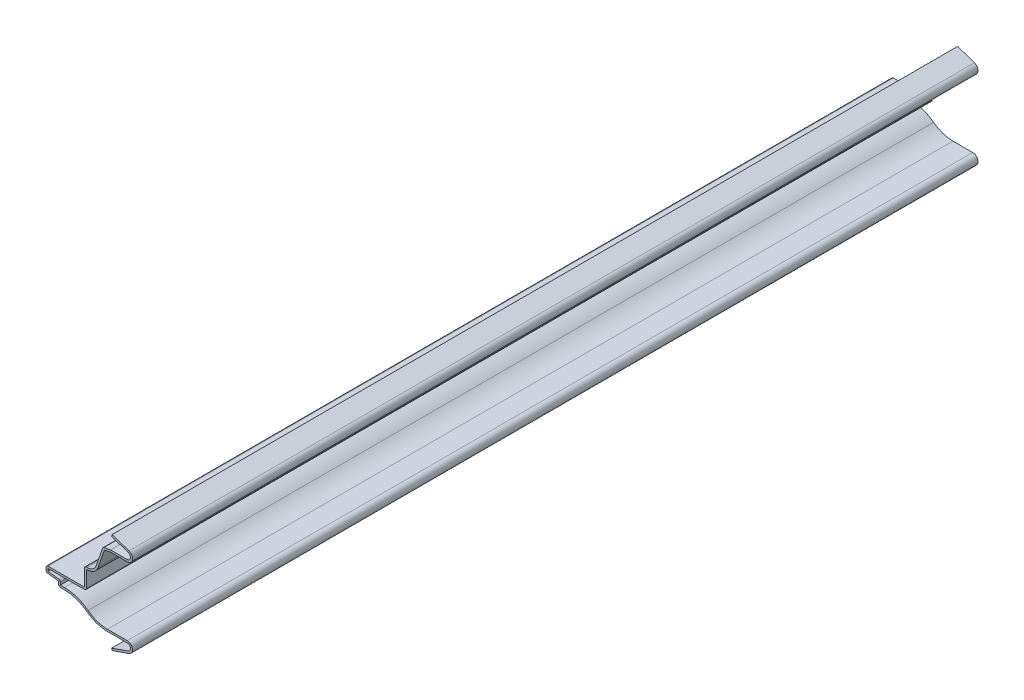
SolidWorks part; units mm, degrees
ref_plane "Front Plane" through (0, 0, 0) normal (0, 0, 1) x (1, 0, 0)
ref_plane "Top Plane" through (0, 0, 0) normal (0, 1, 0) x (1, 0, 0)
ref_plane "Right Plane" through (0, 0, 0) normal (1, 0, 0) x (0, 0, -1)
sketch "Sketch1" plane through (0, 0, 0) normal (0, 0, 1) x (1, 0, 0)
  line L0 (0, 0) -> (0, 50.0063) construction
  line L1 (9.7813, 50.0062) -> (1.1588, 47.0104)
  line L2 (1.7249, 43.6562) -> (10.3187, 43.6562)
  line L3 (10.3187, 43.6562) -> (14.2735, 42.8625)
  line L4 (14.2735, 42.8625) -> (17.7123, 32.9651)
  line L5 (23.7985, 29.7656) -> (23.7985, 20.2406)
  line L6 (23.7985, 20.2406) -> (43.6562, 20.2406)
  line L7 (43.6562, 20.2406) -> (43.6562, 17.0656)
  line L8 (43.6562, 17.0656) -> (37.3062, 16.2719)
  line L9 (37.3062, 16.2719) -> (37.3062, 13.8906)
  line L10 (11.9062, 6.35) -> (10.3187, 6.35)
  line L11 (1.1588, 2.9958) -> (9.7813, 0)
  line L12 (0, 0) -> (9.7813, 0) construction
  line L13 (0, 50.0063) -> (9.7813, 50.0062) construction
  line L14 (0, 25.0031) -> (23.7985, 25.0031) construction
  line L15 (37.3062, 13.8906) -> (34.1312, 13.8906)
  line L16 (10.3187, 6.35) -> (1.7249, 6.35)
  line L17 (23.7985, 29.7656) -> (22.211, 29.7656)
  arc A0 (1.1588, 47.0104) -> (1.7249, 43.6562) centre (1.7249, 45.3811) ccw
  arc A1 (22.211, 29.7656) -> (17.7123, 32.9651) centre (22.211, 34.5281) cw
  arc A2 (34.1312, 13.8906) -> (22.5389, 9.9575) centre (34.1312, -5.1594) ccw
  arc A3 (22.5389, 9.9575) -> (11.9062, 6.35) centre (11.9062, 23.8229) cw
  arc A4 (1.7249, 6.35) -> (1.1588, 2.9958) centre (1.7249, 4.6251) ccw
  arc A5 (1.5293, 7.359) -> (0.787, 2.0497) centre (1.7249, 4.6251) ccw construction
  arc A6 (1.7249, 7.366) -> (0.8253, 2.0361) centre (1.7249, 4.6251) ccw construction
  point P24 (0, 0)
  point P25 (1.3652, 5.6507)
  point P27 (10.3187, 0)
  dimension "D5" = 6.35
  dimension "D6" = 10.3187
  dimension "D14" = 19.05
  dimension "D16" = 4.7625
  dimension "D1" = 37.3062
  dimension "D2" = 0.7937
  dimension "D3" = 9.1281
  dimension "D7" = 9.525
  dimension "D8" = 13.8906
  dimension "D9" = 9.525
  dimension "D10" = 3.175
  dimension "D11" = 0.7937
  dimension "D12" = 3.175
  dimension "D13" = 7.5406
  dimension "D15" = 10.3187
  dimension "D17" = 33.3375
  dimension "D18" = 3.175
  dimension "D19" = 1.5875
  dimension "D20" = 26.9875
  dimension "D21" = 1.5875
  dimension "D4" = 1.016
extrude "Extrude-Thin1" add sketch "Sketch1" against normal blind 436.5625 thin
fillet "Fillet1" radius 1.016 8 edges at (37.3062, 13.8906, -218.2812) (36.2902, 17.1688, -218.2812) (43.6562, 17.0656, -218.2812) (43.6562, 20.2406, -218.2812) (22.7825, 19.2246, -218.2812) (23.7985, 29.7656, -218.2812) (10.3187, 43.6562, -218.2812) (14.2735, 42.8625, -218.2812)
mirror "Mirror1" about plane through (0, 0, 0) normal (1, 0, 0) of bodies 102
delete or keep bodies "Body-Delete/Keep 1" type delete bodies bodies 102
